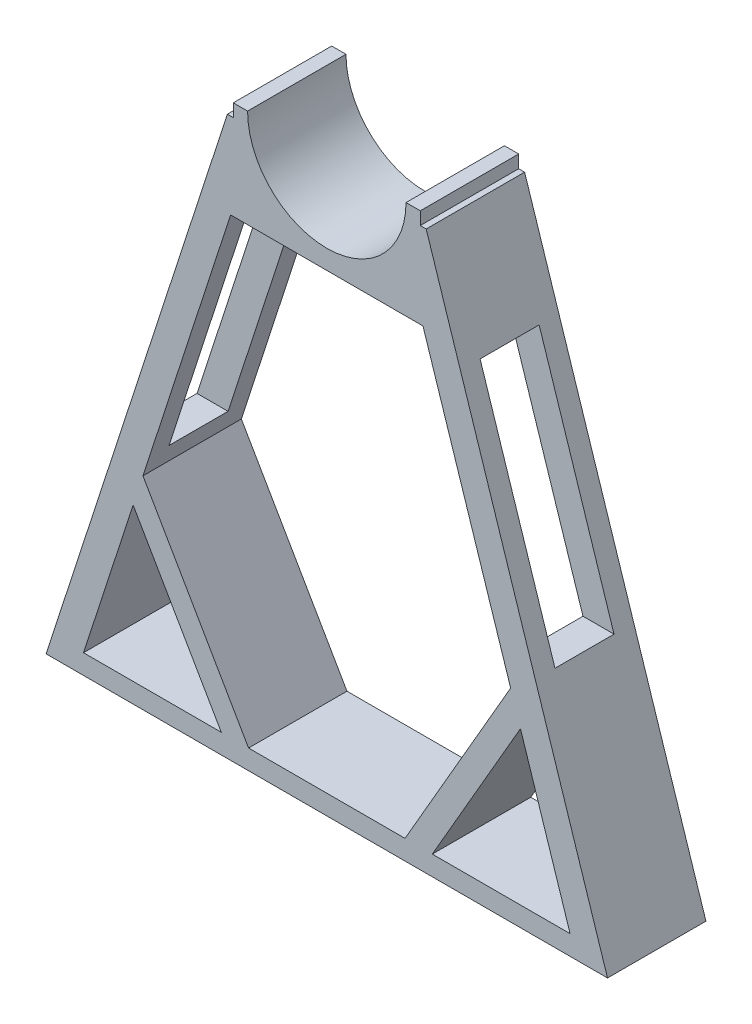
SolidWorks part; units mm, degrees
ref_plane "Front Plane" through (0, 0, 0) normal (0, 0, 1) x (1, 0, 0)
ref_plane "Top Plane" through (0, 0, 0) normal (0, 1, 0) x (1, 0, 0)
ref_plane "Right Plane" through (0, 0, 0) normal (1, 0, 0) x (0, 0, -1)
sketch "Sketch1" plane through (0, 0, 0) normal (0, 0, 1) x (1, 0, 0)
  line L0 (-40.25, 0) -> (-47.5, 0)
  line L1 (-50.5, -6.5) -> (-142.6243, -290)
  line L2 (40.25, 0) -> (47.5, 0)
  line L3 (-142.6243, -290) -> (142.6243, -290)
  line L4 (142.6243, -290) -> (50.5, -6.5)
  line L5 (-47.5, 0) -> (-47.5, -6.5)
  line L6 (47.5, 0) -> (47.5, -6.5)
  line L7 (-47.5, -6.5) -> (-50.5, -6.5)
  line L8 (47.5, -6.5) -> (50.5, -6.5)
  arc A0 (-40.25, 0) -> (40.25, 0) centre (0, 0) ccw
  point P8 (0, -40.25)
  point P15 (0, -290)
  dimension "D1" = 290
  dimension "D2" = 7.25
  dimension "D3" = 6.5
  dimension "D4" = 3
extrude "Boss-Extrude1" add sketch "Sketch1" along normal blind 50
sketch "Sketch2" plane through (0, 0, 50) normal (0, 0, 1) x (1, 0, 0)
  line L0 (-123.6027, -280) -> (-98.3931, -202.4208)
  line L6 (48.8634, -50) -> (93.4028, -187.0641)
  line L7 (123.6027, -280) -> (53.6027, -280)
  line L8 (-142.6243, -290) -> (142.6243, -290) construction
  line L9 (-50.5, -6.5) -> (-142.6243, -290) construction
  line L10 (142.6243, -290) -> (50.5, -6.5) construction
  line L11 (48.8634, -50) -> (-48.8634, -50)
  line L12 (-98.3931, -202.4208) -> (-53.6027, -280)
  line L13 (-93.4028, -187.0641) -> (-39.7463, -280)
  line L14 (98.3931, -202.4208) -> (53.6027, -280)
  line L15 (93.4028, -187.0641) -> (39.7463, -280)
  line L16 (-93.4028, -187.0641) -> (-48.8634, -50)
  line L17 (-53.6027, -280) -> (-123.6027, -280)
  line L18 (39.7463, -280) -> (-39.7463, -280)
  line L19 (98.3931, -202.4208) -> (123.6027, -280)
  dimension "D4" = 50
  dimension "D1" = 15
  dimension "D2" = 10
  dimension "D3" = 15
  dimension "D5" = 60
  dimension "D6" = 60
  dimension "D7" = 12
  dimension "D8" = 12
  dimension "D9" = 70
  dimension "D10" = 70
extrude "Cut-Extrude1" cut sketch "Sketch2" against normal blind 80
ref_plane "Plane1" through (132, 0, 0) normal (1, 0, 0) x (0, 0, -1)
sketch "Sketch4" plane through (132, 0, 0) normal (1, 0, 0) x (0, 0, -1)
  line L0 (0, -50) -> (-50, -50) construction
  line L1 (-40, -60) -> (-10, -60)
  line L2 (-40, -60) -> (-40, -177.0641)
  line L3 (-40, -177.0641) -> (-10, -177.0641)
  line L4 (-10, -60) -> (-10, -177.0641)
  line L5 (0, -290) -> (0, -6.5) construction
  line L6 (0, -187.0641) -> (-50, -187.0641) construction
  line L7 (-50, -290) -> (-50, -6.5) construction
  dimension "D1" = 10
  dimension "D2" = 10
  dimension "D3" = 10
  dimension "D4" = 10
extrude "Cut-Extrude2" cut sketch "Sketch4" against normal blind 260 and the other way through all
